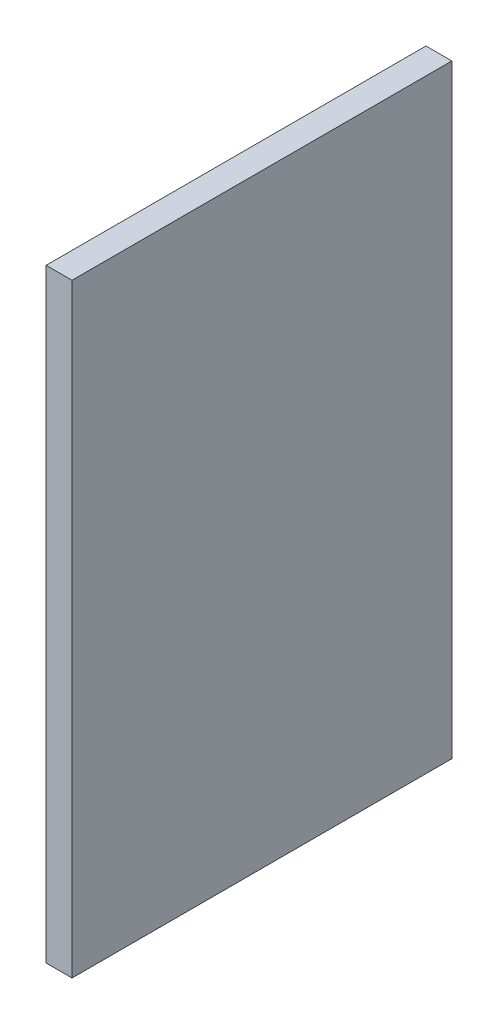
SolidWorks part; units mm, degrees
ref_plane "Plan de face" through (0, 0, 0) normal (0, 0, 1) x (1, 0, 0)
ref_plane "Plan de dessus" through (0, 0, 0) normal (0, 1, 0) x (1, 0, 0)
ref_plane "Plan de droite" through (0, 0, 0) normal (1, 0, 0) x (0, 0, -1)
sketch "Esquisse1" plane through (0, 0, 0) normal (1, 0, 0) x (0, 0, -1)
  line L1 (-110, 175) -> (110, 175)
  line L2 (-110, 175) -> (-110, -175)
  line L3 (-110, -175) -> (110, -175)
  line L4 (110, 175) -> (110, -175)
  line L5 (-110, 175) -> (110, -175) construction
  line L6 (-110, -175) -> (110, 175) construction
  point P0 (0, 0)
  dimension "D1" = 350
  dimension "D2" = 220
extrude "Boss.-Extru.1" add sketch "Esquisse1" along normal blind 15
